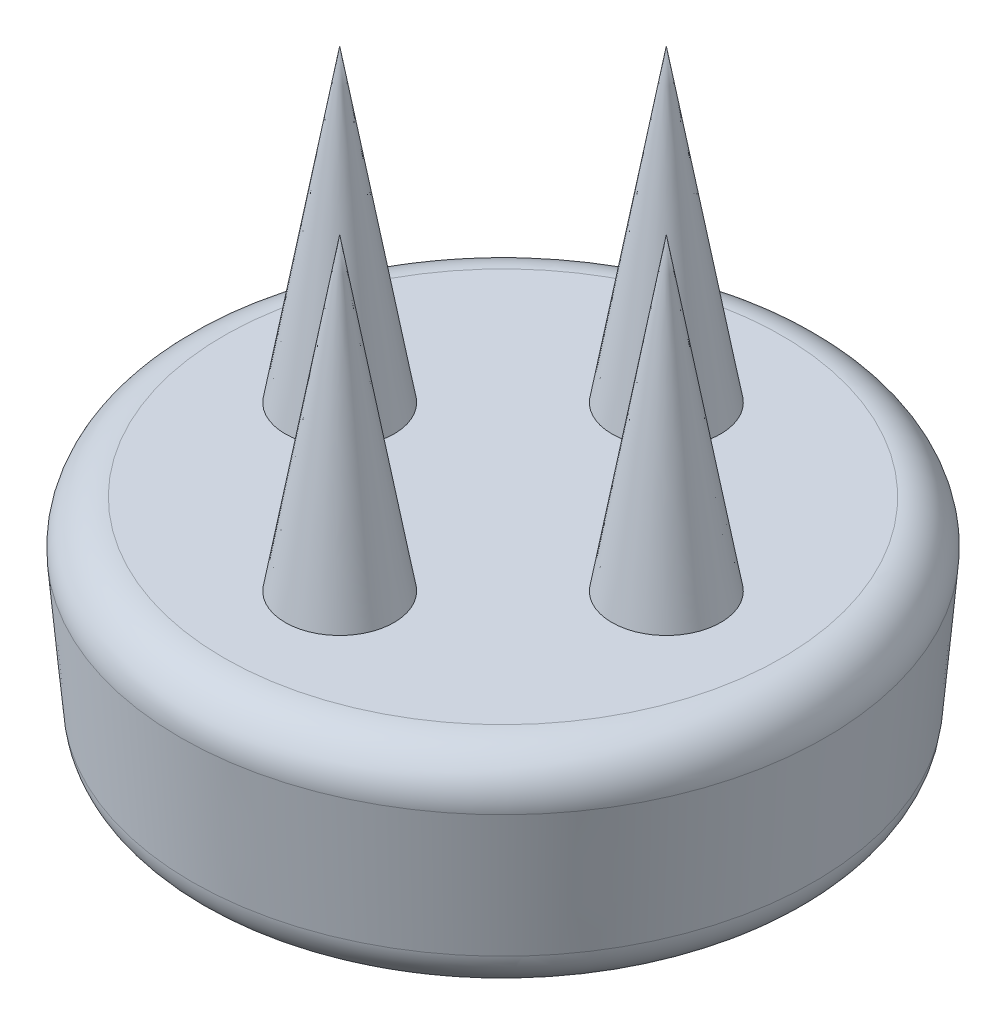
SolidWorks part; units mm, degrees
ref_plane "Front Plane" through (0, 0, 0) normal (0, 0, 1) x (1, 0, 0)
ref_plane "Top Plane" through (0, 0, 0) normal (0, 1, 0) x (1, 0, 0)
ref_plane "Right Plane" through (0, 0, 0) normal (1, 0, 0) x (0, 0, -1)
sketch "Sketch1" plane through (0, 0, 0) normal (0, 1, 0) x (1, 0, 0)
  circle A0 centre (0, 0) radius 15
  dimension "D1" = 30
extrude "Boss-Extrude1" add sketch "Sketch1" against normal blind 10 draft 5
sketch "Sketch2" plane through (0, 0, 0) normal (0, 1, 0) x (1, 0, 0)
  circle A0 centre (0, 7.5) radius 2.5
  circle A1 centre (7.5, 0) radius 2.5
  circle A2 centre (0, -7.5) radius 2.5
  circle A3 centre (-7.5, 0) radius 2.5
  point P10 (0, 0)
  dimension "D1" = 5
  dimension "D2" = 7.5
  dimension "D3" = 4
extrude "Boss-Extrude2" add sketch "Sketch2" along normal blind 15 draft 10
sketch "Sketch3" plane through (0, -10, 0) normal (0, -1, 0) x (-1, 0, 0)
  circle A0 centre (0, 0) radius 5
  dimension "D1" = 10
extrude "Cut-Extrude1" cut sketch "Sketch3" against normal blind 5
fillet "Fillet1" radius 2 2 edges at (0, 0, 15) (0, -10, 14.1251)
